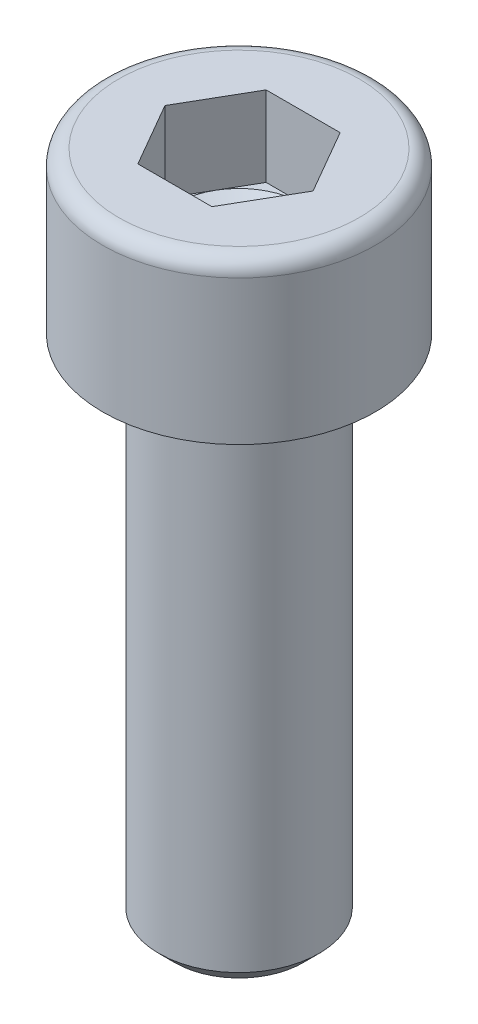
SolidWorks part; units mm, degrees
ref_plane "Plan1" through (0, 0, 0) normal (0, 0, 1) x (1, 0, 0)
ref_plane "Plan2" through (0, 0, 0) normal (0, 1, 0) x (1, 0, 0)
ref_plane "Plan3" through (0, 0, 0) normal (1, 0, 0) x (0, 0, -1)
sketch "Esquisse2" plane through (0, 0, 0) normal (0, 1, 0) x (1, 0, 0)
  circle A0 centre (0, 0) radius 2.5
  dimension "Diamètre nominal" = 5
extrude "Base-Extrusion" add sketch "Esquisse2" against normal blind 16
chamfer "Chanfrein1" distance 0.5 angle 45
sketch "Esquisse5" plane through (0, 0, 0) normal (0, 0, 1) x (1, 0, 0)
  line L0 (-5.75, 0) -> (2.75, 0) construction
  line L1 (2, 5) -> (2, 2.5)
  line L2 (0, 0) -> (4.25, 0)
  line L3 (0, 0) -> (0, 1.3453)
  line L4 (2, 5) -> (3.75, 5)
  line L5 (4.25, 0) -> (4.25, 4.5)
  line L6 (2, 2.5) -> (0, 1.3453)
  line L7 (0, 5) -> (0, -16) construction
  line L8 (0, -15.5) -> (0, 0) construction
  line L9 (-2, -16) -> (2, -16) construction
  line L10 (2, 0) -> (-2, 0) construction
  arc A0 (4.25, 4.5) -> (3.75, 5) centre (3.75, 4.5) ccw
  dimension "D2" = 0.5
  dimension "D1" = 4.25
  dimension "Cote sur plats" = 4
  dimension "D3" = 60
  dimension "D4" = 2.5
  dimension "Diamètre tête" = 8.5
  dimension "Diamètre nominal" = 5
  dimension "D5" = 2
revolve "Boss.-Révol.1" add sketch "Esquisse5" angle 360 about L7
sketch "Esquisse7" plane through (0, 5, 0) normal (0, 1, 0) x (-1, 0, 0)
  line L0 (0, -2) -> (0, 2) construction
  line L1 (0, 0) -> (-1.1547, 2) construction
  line L2 (0, 0) -> (-1.7321, 1) construction
  line L3 (0, 0) -> (-2.3094, 0) construction
  line L4 (1.1547, 2) -> (-1.1547, 2)
  line L5 (-1.1547, 2) -> (-2.3094, 0)
  line L6 (1.1547, -2) -> (-1.1547, -2)
  line L7 (-1.1547, -2) -> (-2.3094, 0)
  line L8 (1.1547, 2) -> (2.3094, 0)
  line L9 (1.1547, -2) -> (2.3094, 0)
  circle A2 centre (0, 0) radius 2 construction
  dimension "D1" = 30
  dimension "D2" = 30
extrude "Enlèv. mat.-Extru.1" cut sketch "Esquisse7" against normal blind 2.5
equation "\"D1@Chanfrein1\" = \"Diamètre nominal@Esquisse2\"*0.1"
equation "\"D1@Esquisse5\" = \"Diamètre tête@Esquisse5\"/2"
equation "\"D2@Esquisse5\" = \"Diamètre nominal@Esquisse5\"*0.1"
equation "\"D4@Esquisse5\" = \"Diamètre nominal@Esquisse5\"/2"
equation "\"D5@Esquisse5\" = \"Cote sur plats@Esquisse5\"/2"
equation "\"D1@Enlèv. mat.-Extru.1\" = \"Diamètre nominal@Esquisse5\"/2"
